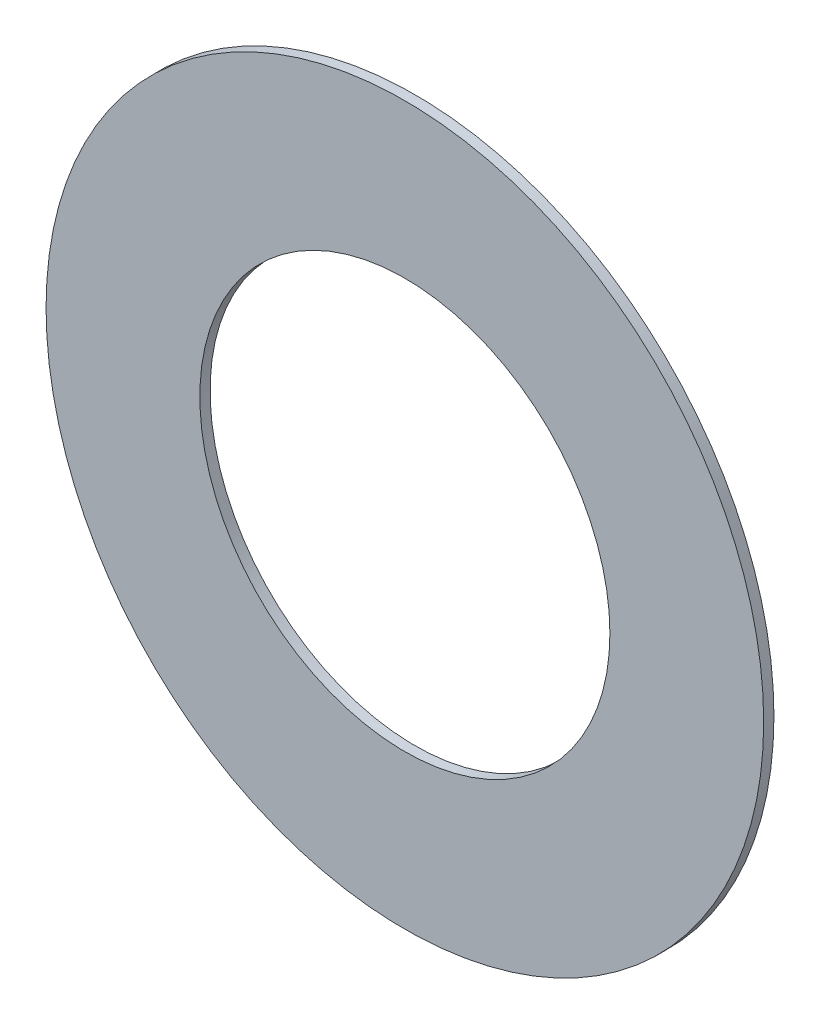
SolidWorks part; units mm, degrees
ref_plane "Front" through (0, 0, 0) normal (0, 0, 1) x (1, 0, 0)
ref_plane "Top" through (0, 0, 0) normal (0, 1, 0) x (1, 0, 0)
ref_plane "Right" through (0, 0, 0) normal (1, 0, 0) x (0, 0, -1)
sketch "Sketch1" plane through (0, 0, 0) normal (0, 0, 1) x (1, 0, 0)
  circle A0 centre (0, 0) radius 3.5
  circle A1 centre (0, 0) radius 2
  dimension "D1" = 4
  dimension "D2" = 7
extrude "Boss-Extrude1" add sketch "Sketch1" along normal blind 0.1
